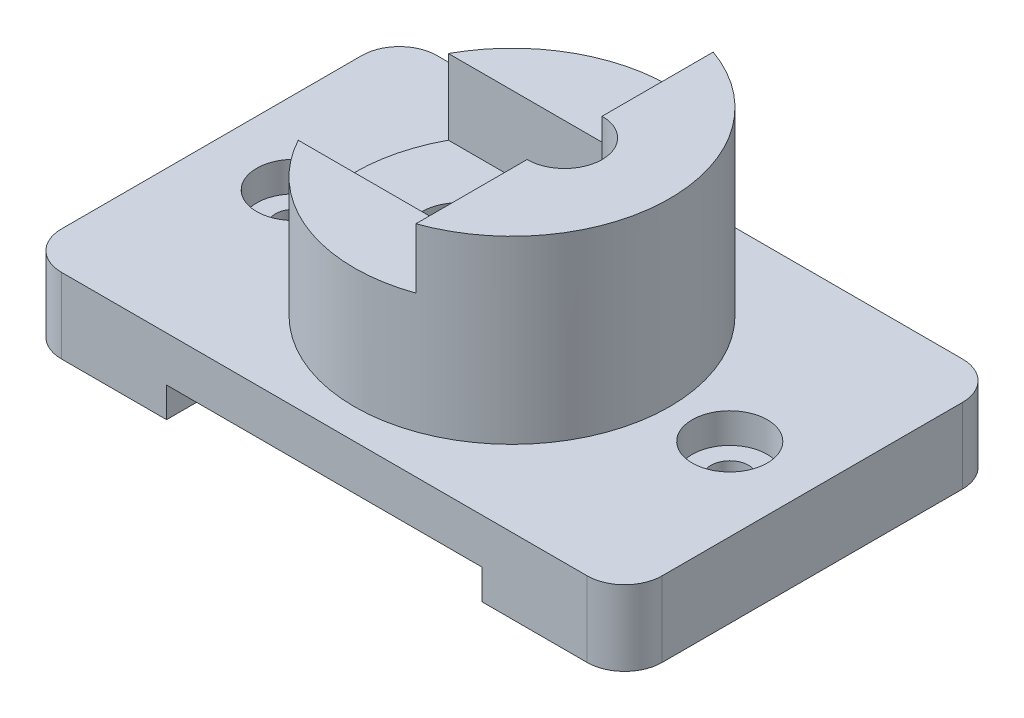
SolidWorks part; units mm, degrees
ref_plane "前视基准面" through (0, 0, 0) normal (0, 0, 1) x (1, 0, 0)
ref_plane "上视基准面" through (0, 0, 0) normal (0, 1, 0) x (1, 0, 0)
ref_plane "右视基准面" through (0, 0, 0) normal (1, 0, 0) x (0, 0, -1)
sketch "草图1" plane through (0, 0, 0) normal (0, 1, 0) x (1, 0, 0)
  line L0 (-55, 0) -> (55, 0) construction
  line L1 (-35, 25) -> (35, 25)
  line L2 (-40, 20) -> (-40, -20)
  line L3 (-35, -25) -> (35, -25)
  line L4 (40, 20) -> (40, -20)
  arc A0 (-35, -25) -> (-40, -20) centre (-35, -20) cw
  arc A1 (40, -20) -> (35, -25) centre (35, -20) cw
  arc A2 (35, 25) -> (40, 20) centre (35, 20) cw
  arc A3 (-35, 25) -> (-40, 20) centre (-35, 20) ccw
  point P6 (22.7837, 7.1809)
  point P10 (-40, -25)
  point P13 (40, -25)
  point P16 (40, 25)
  point P19 (-40, 25)
  dimension "D5" = 5
  dimension "D1" = 50
  dimension "D2" = 80
  dimension "D3" = 25
  dimension "D4" = 40
extrude "凸台-拉伸1" add sketch "草图1" along normal blind 10
sketch "草图2" plane through (0, 0, 0) normal (0, 1, 0) x (1, 0, 0)
  circle A0 centre (0, 0) radius 21
  dimension "D1" = 42
extrude "凸台-拉伸2" add sketch "草图2" along normal blind 34
sketch "草图3" plane through (0, 34, 0) normal (0, 1, 0) x (1, 0, 0)
  line L0 (-18.7, 0) -> (18.7, 0) construction
  line L1 (0, -18.7) -> (0, 18.7) construction
  line L2 (-7, 5) -> (7, 5)
  line L3 (7, -5) -> (-7, -5)
  arc A0 (7, -5) -> (7, 5) centre (7, 0) ccw
  arc A1 (-7, -5) -> (-7, 5) centre (-7, 0) cw
  dimension "D1" = 10
  dimension "D2" = 7
extrude "切除-拉伸1" cut sketch "草图3" against normal through all
sketch "草图4" plane through (0, 34, 0) normal (0, 1, 0) x (1, 0, 0)
  line L0 (7, 19.799) -> (7, -19.799)
  line L1 (0, -18.7) -> (0, 18.7) construction
  circle A0 centre (0, 0) radius 21 construction
  arc A2 (7, 19.799) -> (7, -19.799) centre (0, 0) ccw
  dimension "D1" = 7
extrude "切除-拉伸2" cut sketch "草图4" against normal blind 8
sketch "草图5" plane through (0, 26, 0) normal (0, 1, 0) x (1, 0, 0)
  line L0 (-18.4662, 10) -> (7, 10)
  line L1 (7, 5) -> (7, 19.799) construction
  line L2 (7, 10) -> (7, -10)
  line L3 (7, -19.799) -> (7, -5) construction
  line L4 (7, -10) -> (-18.4662, -10)
  arc A0 (7, 19.799) -> (7, -19.799) centre (0, 0) ccw construction
  arc A1 (-18.4662, 10) -> (-18.4662, -10) centre (0, 0) ccw
  point P11 (-66.8871, 5.6293)
  dimension "D1" = 10
  dimension "D2" = 20
extrude "切除-拉伸3" cut sketch "草图5" against normal blind 10
sketch "草图6" plane through (0, 10, 0) normal (0, 1, 0) x (1, 0, 0)
  line L0 (-18.7, 0) -> (18.7, 0) construction
  line L1 (0, -18.7) -> (0, 18.7) construction
  circle A0 centre (-29, 0) radius 5
  dimension "D1" = 10
  dimension "D2" = 29
extrude "切除-拉伸4" cut sketch "草图6" against normal blind 4 contours A0
sketch "草图7" plane through (0, 6, 0) normal (0, 1, 0) x (1, 0, 0)
  circle A0 centre (-29, 0) radius 2.5
  dimension "D1" = 5
extrude "切除-拉伸5" cut sketch "草图7" against normal through all
mirror "镜向1" about plane through (0, 0, 0) normal (1, 0, 0) of "切除-拉伸4", "切除-拉伸5"
sketch "草图8" plane through (0, 0, 0) normal (0, 0, 1) x (1, 0, 0)
  line L0 (27.5, 0) -> (-27.5, 0) construction
  line L1 (21, 0) -> (-21, 0)
  line L2 (21, 0) -> (21, 4)
  line L3 (21, 4) -> (-21, 4)
  line L4 (-21, 0) -> (-21, 4)
  dimension "D1" = 42
  dimension "D2" = 4
  dimension "D3" = 21
extrude "切除-拉伸6" cut sketch "草图8" against normal through all and the other way through all
